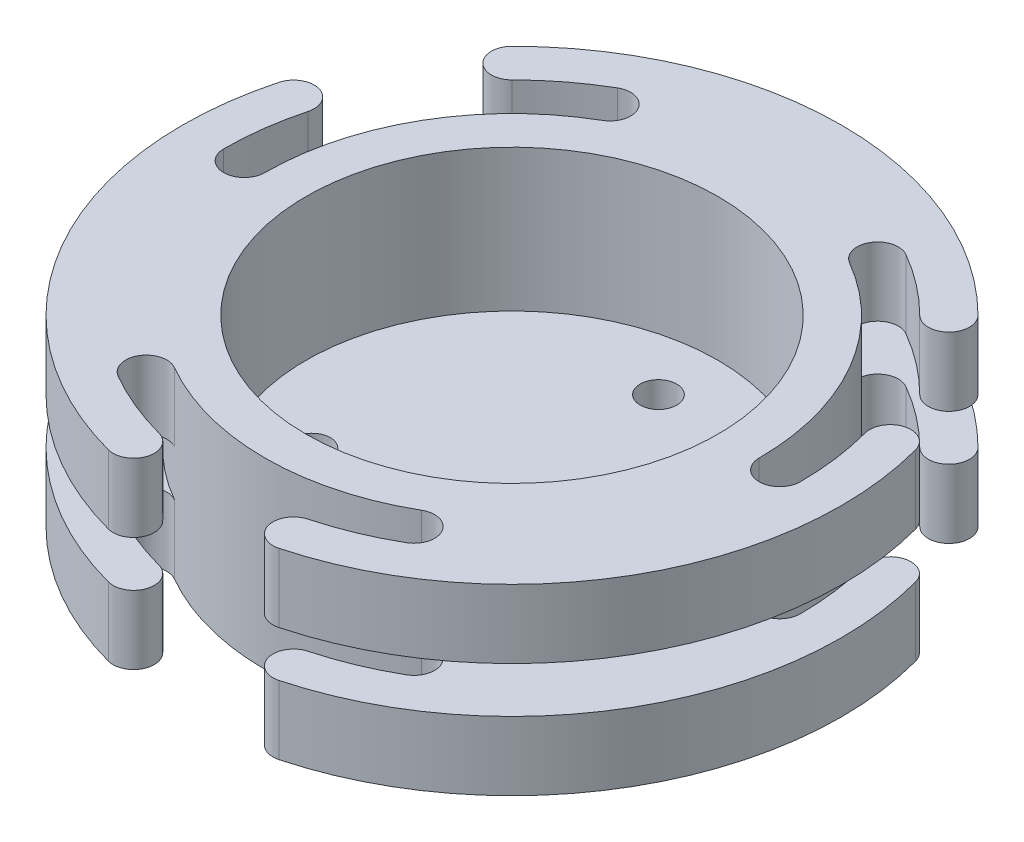
SolidWorks part; units mm, degrees
material "Nylon 101"
ref_plane "Plan de face" through (0, 0, 0) normal (0, 0, 1) x (1, 0, 0)
ref_plane "Plan de dessus" through (0, 0, 0) normal (0, 1, 0) x (1, 0, 0)
ref_plane "Plan de droite" through (0, 0, 0) normal (1, 0, 0) x (0, 0, -1)
sketch "Esquisse1" plane through (0, 0, 0) normal (0, 1, 0) x (1, 0, 0)
  circle A0 centre (0, 0) radius 22.5
  circle A1 centre (0, 0) radius 40 construction
  circle A2 centre (0, 0) radius 36 construction
  circle A3 centre (0, 0) radius 31.5
  circle A4 centre (0, 0) radius 27 construction
  dimension "D1" = 45
  dimension "D2" = 80
  dimension "D3" = 72
  dimension "D4" = 63
  dimension "D5" = 54
extrude "Boss.-Extru.1" add sketch "Esquisse1" along normal blind 20
sketch "Esquisse2" plane through (0, 20, 0) normal (0, 1, 0) x (1, 0, 0)
  line L0 (-14.625, 25.3312) -> (0, 0) construction
  line L1 (0, 0) -> (-29.25, 0) construction
  line L2 (0, 0) -> (0, 31.5) construction
  arc A0 (-29.25, 0) -> (-14.625, 25.3312) centre (0, 0) cw construction
  arc A1 (-15.75, 27.2798) -> (-31.5, 0) centre (0, 0) ccw
  arc A2 (-13.5, 23.3827) -> (-27, 0) centre (0, 0) ccw
  arc A3 (-13.5, 23.3827) -> (-15.75, 27.2798) centre (-14.625, 25.3312) ccw
  arc A4 (-31.5, 0) -> (-27, 0) centre (-29.25, 0) ccw
  circle A5 centre (0, 0) radius 31.5 construction
  arc A6 (14.625, 25.3312) -> (29.25, 0) centre (0, 0) cw construction
  arc A7 (31.5, 0) -> (15.75, 27.2798) centre (0, 0) ccw
  arc A8 (27, 0) -> (13.5, 23.3827) centre (0, 0) ccw
  arc A9 (27, 0) -> (31.5, 0) centre (29.25, 0) ccw
  arc A10 (15.75, 27.2798) -> (13.5, 23.3827) centre (14.625, 25.3312) ccw
  arc A11 (14.625, -25.3312) -> (-14.625, -25.3312) centre (0, 0) cw construction
  arc A12 (-15.75, -27.2798) -> (15.75, -27.2798) centre (0, 0) ccw
  arc A13 (-13.5, -23.3827) -> (13.5, -23.3827) centre (0, 0) ccw
  arc A14 (-13.5, -23.3827) -> (-15.75, -27.2798) centre (-14.625, -25.3312) ccw
  arc A15 (15.75, -27.2798) -> (13.5, -23.3827) centre (14.625, -25.3312) ccw
  point P4 (-25.3312, 14.625)
  point P21 (25.3312, 14.625)
  point P28 (0, -29.25)
  point P33 (0, 0)
  dimension "D1" = 2.25
  dimension "D2" = 60
  dimension "D3" = 30
  dimension "D4" = 3
extrude "Enlèv. mat.-Extru.1" cut sketch "Esquisse2" against normal through all
sketch "Esquisse3" plane through (0, 20, 0) normal (0, 1, 0) x (1, 0, 0)
  line L0 (0, 33.75) -> (0, 0) construction
  line L1 (-23.8649, 23.8649) -> (0, 0) construction
  arc A0 (-23.8649, 23.8649) -> (23.8649, 23.8649) centre (0, 0) cw construction
  arc A1 (25.4558, 25.4558) -> (-25.4558, 25.4558) centre (0, 0) ccw
  arc A2 (22.2739, 22.2739) -> (-22.2739, 22.2739) centre (0, 0) ccw
  arc A3 (22.2739, 22.2739) -> (25.4558, 25.4558) centre (23.8649, 23.8649) ccw
  arc A4 (-25.4558, 25.4558) -> (-22.2739, 22.2739) centre (-23.8649, 23.8649) ccw
  arc A5 (15.75, 27.2798) -> (-15.75, 27.2798) centre (0, 0) ccw construction
  arc A6 (32.6, 8.7351) -> (8.7351, -32.6) centre (0, 0) cw construction
  arc A7 (9.3175, -34.7733) -> (34.7733, 9.3175) centre (0, 0) ccw
  arc A8 (8.1528, -30.4267) -> (30.4267, 8.1528) centre (0, 0) ccw
  arc A9 (8.1528, -30.4267) -> (9.3175, -34.7733) centre (8.7351, -32.6) ccw
  arc A10 (34.7733, 9.3175) -> (30.4267, 8.1528) centre (32.6, 8.7351) ccw
  arc A11 (-8.7351, -32.6) -> (-32.6, 8.7351) centre (0, 0) cw construction
  arc A12 (-34.7733, 9.3175) -> (-9.3175, -34.7733) centre (0, 0) ccw
  arc A13 (-30.4267, 8.1528) -> (-8.1528, -30.4267) centre (0, 0) ccw
  arc A14 (-30.4267, 8.1528) -> (-34.7733, 9.3175) centre (-32.6, 8.7351) ccw
  arc A15 (-9.3175, -34.7733) -> (-8.1528, -30.4267) centre (-8.7351, -32.6) ccw
  point P4 (0, 33.75)
  point P19 (29.2284, -16.875)
  point P26 (-29.2284, -16.875)
  point P31 (0, 0)
  dimension "D1" = 2.25
  dimension "D2" = 45
extrude "Boss.-Extru.2" add sketch "Esquisse3" against normal up to surface (20 mm away) up to face at (0, 0, 0)
sketch "Esquisse4" plane through (0, 0, 0) normal (0, -1, 0) x (1, 0, 0)
  circle A0 centre (0, 0) radius 22.5
extrude "Boss.-Extru.3" add sketch "Esquisse4" against normal blind 4.5
sketch "Esquisse5" plane through (0, 4.5, 0) normal (0, 1, 0) x (1, 0, 0)
  line L0 (0, 0) -> (0, 16) construction
  circle A0 centre (0, 16) radius 2
  circle A1 centre (13.8564, -8) radius 2
  circle A2 centre (-13.8564, -8) radius 2
  point P12 (0, 0)
  dimension "D2" = 4
  dimension "D1" = 16
  dimension "D3" = 3
extrude "Enlèv. mat.-Extru.2" cut sketch "Esquisse5" against normal up to next
sketch "Esquisse6" plane through (0, 0, 0) normal (1, 0, 0) x (0, 0, -1)
  line L0 (36, 10) -> (0, 10) construction
  line L1 (36, 12.5) -> (27, 12.5)
  line L2 (36, 12.5) -> (36, 7.5)
  line L3 (36, 7.5) -> (27, 7.5)
  line L4 (27, 12.5) -> (27, 7.5)
  line L5 (0, 10) -> (0, 0) construction
  dimension "D1" = 10
  dimension "D2" = 9
  dimension "D3" = 36
  dimension "D4" = 5
revolve "Enlèvement de matière-Révolution1" cut sketch "Esquisse6" angle 360 about L5
